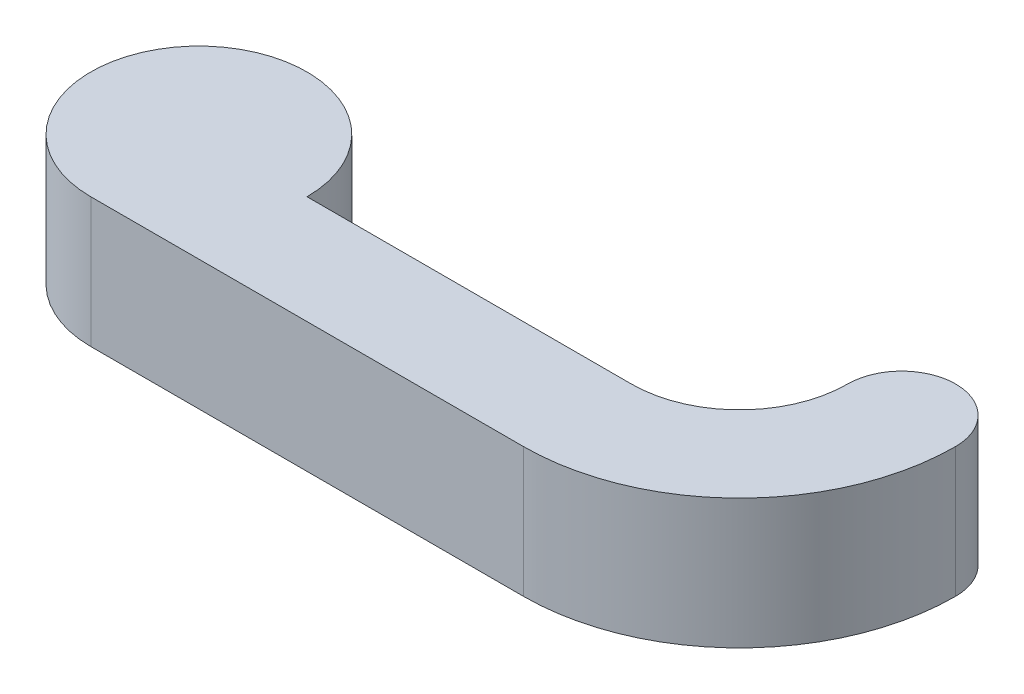
SolidWorks part; units mm, degrees
ref_plane "Front Plane" through (0, 0, 0) normal (0, 0, 1) x (1, 0, 0)
ref_plane "Top Plane" through (0, 0, 0) normal (0, 1, 0) x (1, 0, 0)
ref_plane "Right Plane" through (0, 0, 0) normal (1, 0, 0) x (0, 0, -1)
sketch "Sketch1" plane through (0, 0, 0) normal (0, 1, 0) x (1, 0, 0)
  line L0 (0, 0) -> (20, 0)
  line L1 (0, -5) -> (20, -5)
  circle A0 centre (0, 0) radius 5
  arc A1 (20, 0) -> (25, 5) centre (20, 5) ccw
  arc A2 (20, -5) -> (30, 5) centre (20, 5) ccw
  arc A3 (25, 5) -> (30, 5) centre (27.5, 5) cw
  point P11 (0, 0)
  point P12 (0, 0)
  dimension "D1" = 10
  dimension "D2" = 5
  dimension "D3" = 20
  dimension "D4" = 5
extrude "Boss-Extrude2" add sketch "Sketch1" along normal mid plane 6
sketch "Sketch4" plane through (0, -3, 0) normal (0, -1, 0) x (1, 0, 0)
  circle A0 centre (0, 0) radius 3
  dimension "D1" = 6
extrude "Cut-Extrude2" cut sketch "Sketch4" against normal blind 2.5
